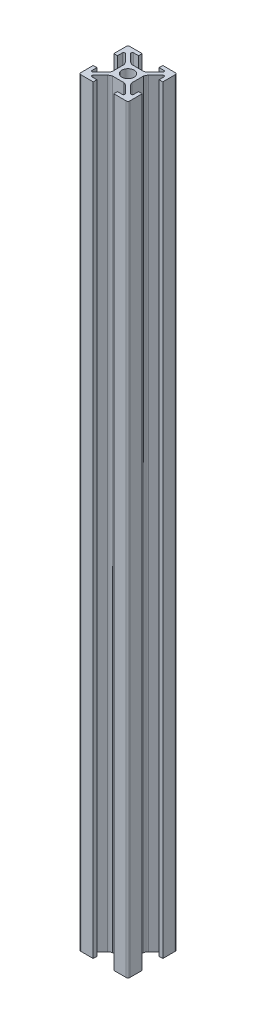
SolidWorks part; units mm, degrees
ref_plane "Front Plane" through (0, 0, 0) normal (0, 0, 1) x (1, 0, 0)
ref_plane "Top Plane" through (0, 0, 0) normal (0, 1, 0) x (1, 0, 0)
ref_plane "Right Plane" through (0, 0, 0) normal (1, 0, 0) x (0, 0, -1)
sketch "Sketch1" plane through (0, 0, 0) normal (0, 1, 0) x (1, 0, 0)
  line L0 (-3.611, 4.6716) -> (-6.5858, 7.6464)
  line L1 (9.25, -10) -> (4.2, -10)
  line L2 (10, -9.25) -> (10, -4.2)
  line L3 (9.25, 10) -> (4.2, 10)
  line L4 (-10, -9.25) -> (-10, -4.2)
  line L5 (10, -10) -> (-10, 10) construction
  line L6 (10, 10) -> (-10, -10) construction
  line L7 (2.2681, -4) -> (-2.2681, -4)
  line L8 (4, -2.2681) -> (4, 2.2681)
  line L9 (2.2681, 4) -> (-2.2681, 4)
  line L10 (-4, -2.2681) -> (-4, 2.2681)
  line L11 (4, -4) -> (-4, 4) construction
  line L12 (4, 4) -> (-4, -4) construction
  line L13 (-6.2322, 8.5) -> (-4.2, 8.5)
  line L14 (-4.2, 8.5) -> (-4.2, 10)
  line L15 (4.6716, 3.611) -> (7.6464, 6.5858)
  line L16 (8.5, 6.2322) -> (8.5, 4.2)
  line L17 (8.5, 4.2) -> (10, 4.2)
  line L18 (4.2, 8.5) -> (4.2, 10)
  line L19 (-8.5, 4.2) -> (-10, 4.2)
  line L20 (-8.5, 6.2322) -> (-8.5, 4.2)
  line L21 (-4.6716, 3.611) -> (-7.6464, 6.5858)
  line L22 (0, 10) -> (0, -10) construction
  line L23 (6.2322, 8.5) -> (4.2, 8.5)
  line L24 (3.611, 4.6716) -> (6.5858, 7.6464)
  line L25 (-55, 0) -> (55, 0) construction
  line L26 (3.611, -4.6716) -> (6.5858, -7.6464)
  line L27 (6.2322, -8.5) -> (4.2, -8.5)
  line L28 (-4.6716, -3.611) -> (-7.6464, -6.5858)
  line L29 (-8.5, -6.2322) -> (-8.5, -4.2)
  line L30 (-8.5, -4.2) -> (-10, -4.2)
  line L31 (4.2, -8.5) -> (4.2, -10)
  line L32 (8.5, -4.2) -> (10, -4.2)
  line L33 (8.5, -6.2322) -> (8.5, -4.2)
  line L34 (4.6716, -3.611) -> (7.6464, -6.5858)
  line L35 (-4.2, -8.5) -> (-4.2, -10)
  line L36 (-6.2322, -8.5) -> (-4.2, -8.5)
  line L37 (2.2681, -4) -> (-2.2681, -4)
  line L38 (10, -10) -> (4.2, -10)
  line L39 (-3.611, -4.6716) -> (-6.5858, -7.6464)
  line L40 (-4.2, 10) -> (-9.25, 10)
  line L41 (-10, 4.2) -> (-10, 9.25)
  line L42 (-4.2, -10) -> (-9.25, -10)
  line L43 (-4.2, -10) -> (-10, -10)
  line L44 (10, 4.2) -> (10, 9.25)
  circle A0 centre (0, 0) radius 2.5
  arc A1 (-8.5, 6.2322) -> (-7.6464, 6.5858) centre (-8, 6.2322) cw
  arc A2 (-6.5858, 7.6464) -> (-6.2322, 8.5) centre (-6.2322, 8) cw
  arc A3 (-3.611, 4.6716) -> (-2.2681, 4) centre (-1.7294, 6.7555) ccw
  arc A4 (-4.6716, 3.611) -> (-4, 2.2681) centre (-6.7555, 1.7294) cw
  arc A5 (4.6716, 3.611) -> (4, 2.2681) centre (6.7555, 1.7294) ccw
  arc A6 (3.611, 4.6716) -> (2.2681, 4) centre (1.7294, 6.7555) cw
  arc A7 (6.5858, 7.6464) -> (6.2322, 8.5) centre (6.2322, 8) ccw
  arc A8 (8.5, 6.2322) -> (7.6464, 6.5858) centre (8, 6.2322) ccw
  arc A9 (8.5, -6.2322) -> (7.6464, -6.5858) centre (8, -6.2322) cw
  arc A10 (6.5858, -7.6464) -> (6.2322, -8.5) centre (6.2322, -8) cw
  arc A11 (3.611, -4.6716) -> (2.2681, -4) centre (1.7294, -6.7555) ccw
  arc A12 (4.6716, -3.611) -> (4, -2.2681) centre (6.7555, -1.7294) cw
  arc A13 (-4.6716, -3.611) -> (-4, -2.2681) centre (-6.7555, -1.7294) ccw
  arc A14 (-3.611, -4.6716) -> (-2.2681, -4) centre (-1.7294, -6.7555) cw
  arc A15 (-6.5858, -7.6464) -> (-6.2322, -8.5) centre (-6.2322, -8) ccw
  arc A16 (-8.5, -6.2322) -> (-7.6464, -6.5858) centre (-8, -6.2322) ccw
  arc A17 (-9.25, -10) -> (-10, -9.25) centre (-9.25, -9.25) cw
  arc A18 (9.25, -10) -> (10, -9.25) centre (9.25, -9.25) ccw
  arc A19 (10, 9.25) -> (9.25, 10) centre (9.25, 9.25) ccw
  arc A20 (-9.25, 10) -> (-10, 9.25) centre (-9.25, 9.25) ccw
  point P0 (0, 0)
  point P18 (-8.5, 7.4393)
  point P24 (-7.4393, 8.5)
  point P50 (7.4393, 8.5)
  point P51 (8.5, 7.4393)
  point P86 (8.5, -7.4393)
  point P87 (7.4393, -8.5)
  point P88 (-7.4393, -8.5)
  point P89 (-8.5, -7.4393)
  dimension "D2" = 5
  dimension "D7" = 0.5
  dimension "D8" = 0.75
  dimension "D1" = 20
  dimension "D3" = 8
  dimension "D4" = 1.5
  dimension "D5" = 1.5
  dimension "D6" = 8.4
extrude "Boss-Extrude1" add sketch "Sketch1" along normal blind 310 contours L40 A20 L41 L19 L20 A1 L21 A4 L10 A13 L28 A16 L29 L30 L4 A17 L42 L35 L36 A15 L39 A14 L7 A11 L26 A10 L27 L31 L1 A18 L2 L32 L33 A9 L34 A12 L8 A5 L15 A8 L16 L17 L44 A19 L3 L18 L23 A7 L24 A6 L9
